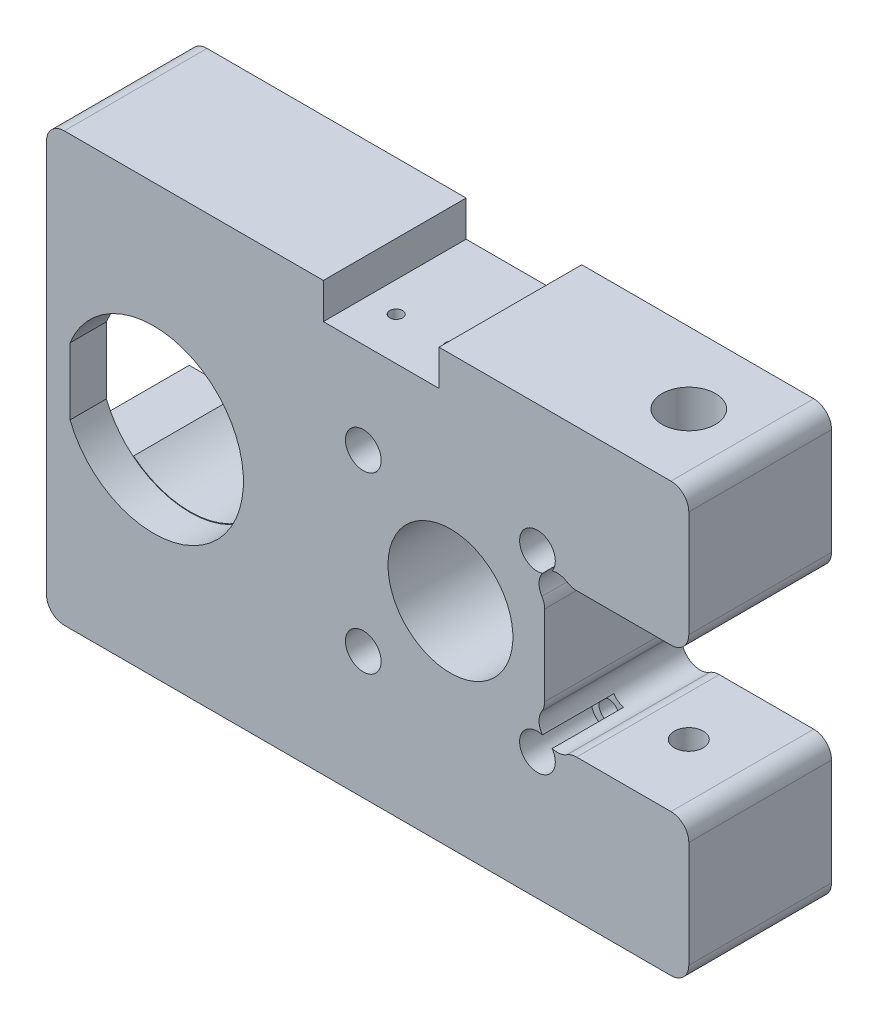
SolidWorks part; units mm, degrees
ref_plane "Front Plane" through (0, 0, 0) normal (0, 0, 1) x (1, 0, 0)
ref_plane "Top Plane" through (0, 0, 0) normal (0, 1, 0) x (1, 0, 0)
ref_plane "Right Plane" through (0, 0, 0) normal (1, 0, 0) x (0, 0, -1)
sketch "Sketch1" plane through (0, 0, 0) normal (0, 0, 1) x (1, 0, 0)
  line L1 (57.15, -38.1) -> (-57.15, -38.1)
  line L2 (57.15, -38.1) -> (57.15, 38.1)
  line L3 (57.15, 38.1) -> (-57.15, 38.1)
  line L4 (-57.15, -38.1) -> (-57.15, 38.1)
  line L5 (57.15, -38.1) -> (-57.15, 38.1) construction
  line L6 (57.15, 38.1) -> (-57.15, -38.1) construction
  point P0 (0, 0)
  dimension "D1" = 76.2
  dimension "D2" = 114.3
extrude "Boss-Extrude1" add sketch "Sketch1" along normal blind 25.4
sketch "Sketch2" plane through (0, 0, 25.4) normal (0, 0, 1) x (1, 0, 0)
  line L0 (-57.15, 38.1) -> (-57.15, -38.1) construction
  line L1 (57.15, 38.1) -> (-57.15, 38.1) construction
  line L2 (-53.975, 38.1) -> (-53.975, -38.1) construction
  line L3 (-57.15, -38.1) -> (57.15, -38.1) construction
  line L5 (-52.959, 5.9392) -> (-52.959, -5.9392)
  circle A1 centre (-38.1, 0) radius 15.875 construction
  arc A2 (-52.959, -5.9392) -> (-52.959, 5.9392) centre (-38.1, 0) ccw
  dimension "D2" = 16.002
  dimension "D3" = 31.75
  dimension "D4" = 1.016
  dimension "D1" = 3.175
extrude "Cut-Extrude1" cut sketch "Sketch2" against normal blind 6.477
sketch "Sketch3" plane through (0, 0, 18.923) normal (0, 0, 1) x (1, 0, 0)
  line L0 (-54.445, 0) -> (53.1859, 0) construction
  line L1 (-15.0726, 9.9464) -> (-12.8275, 12.1915) construction
  line L2 (-17.2768, 12.319) -> (-28.067, 12.319)
  line L3 (-57.15, 38.1) -> (-57.15, -38.1) construction
  line L4 (-15.0726, -9.9464) -> (-12.8275, -12.1915) construction
  line L5 (-48.133, -12.319) -> (-57.15, -12.319)
  line L6 (-17.2768, -12.319) -> (-28.067, -12.319)
  line L7 (-15.0726, 9.9464) -> (-23.9041, 9.9464) construction
  line L8 (-48.133, 12.319) -> (-57.15, 12.319)
  line L9 (-12.7, 7.7422) -> (-12.7, 13.9418) construction
  line L10 (-57.15, -12.319) -> (-57.15, 12.319)
  line L11 (-12.7, 7.7422) -> (-12.7, -7.7422)
  line L12 (-17.2768, 12.319) -> (-12.7, 12.319) construction
  line L13 (-12.7, 12.319) -> (-15.0726, 9.9464) construction
  arc A0 (-28.067, 12.319) -> (-48.133, 12.319) centre (-38.1, 0) ccw
  arc A1 (-12.7, 7.7422) -> (-17.2768, 12.319) centre (-15.0726, 9.9464) ccw
  arc A2 (-12.7, -7.7422) -> (-17.2768, -12.319) centre (-15.0726, -9.9464) cw
  arc A3 (-28.067, -12.319) -> (-48.133, -12.319) centre (-38.1, 0) cw
  point P3 (-31.623, 25.4)
  point P17 (-31.623, -25.4)
  point P23 (-12.7, 0)
  point P24 (-57.15, 0)
  dimension "D5" = 6.477
  dimension "D1" = 12.319
  dimension "D2" = 15.24
  dimension "D3" = 9.017
  dimension "D4" = 45
  dimension "D6" = 3.175
  dimension "D7" = 44.45
extrude "Cut-Extrude2" cut sketch "Sketch3" against normal up to vertex (18.923 mm away)
sketch "Sketch4" plane through (0, 38.1, 0) normal (0, 1, 0) x (1, 0, 0)
  line L0 (12.7, -25.4) -> (12.7, 0) construction
  line L1 (57.15, -25.4) -> (-57.15, -25.4) construction
  line L2 (57.15, 0) -> (-57.15, 0) construction
  line L3 (57.15, -25.4) -> (57.15, 0) construction
  line L5 (-7.874, 0) -> (12.7, 0)
  line L6 (-7.874, 0) -> (-7.874, -25.4)
  line L7 (-7.874, -25.4) -> (12.7, -25.4)
  line L8 (12.7, 0) -> (12.7, -25.4)
  line L9 (-7.874, 0) -> (12.7, -25.4) construction
  line L10 (-7.874, -25.4) -> (12.7, 0) construction
  point P8 (2.413, -12.7)
  dimension "D1" = 44.45
  dimension "D2" = 20.574
extrude "Cut-Extrude3" cut sketch "Sketch4" against normal blind 6.35
sketch "Sketch5" plane through (0, 0, 0) normal (0, 0, -1) x (-1, 0, 0)
  line L0 (0, 0) -> (-57.15, 0) construction
  line L2 (-57.15, -38.1) -> (-57.15, 38.1) construction
  line L3 (-33.7411, 10.5819) -> (-33.7411, -10.5819) construction
  line L4 (-36.0751, -12.827) -> (-57.15, -12.827)
  line L5 (-31.496, -8.2479) -> (-31.496, 8.2479)
  line L6 (-36.0751, 12.827) -> (-57.15, 12.827)
  line L7 (-57.15, -12.827) -> (-57.15, 12.827)
  line L8 (-31.496, -12.827) -> (-57.15, 12.827) construction
  line L9 (-31.496, 12.827) -> (-57.15, -12.827) construction
  line L10 (-57.15, 38.1) -> (-12.7, 38.1) construction
  line L11 (38.1, 0) -> (38.1, 30.2258) construction
  arc A0 (-36.0751, -12.827) -> (-31.496, -8.2479) centre (-33.7411, -10.5819) ccw
  arc A2 (-31.496, 8.2479) -> (-36.0751, 12.827) centre (-33.7411, 10.5819) ccw
  point P4 (-44.323, 0)
  dimension "D4" = 3.175
  dimension "D5" = 25.654
  dimension "D3" = 27.5181
  dimension "D1" = 25.654
  dimension "D2" = 25.654
  dimension "D6" = 23.4089
  dimension "D7" = 69.596
extrude "Cut-Extrude4" cut sketch "Sketch5" against normal up to vertex
sketch "Sketch6" plane through (0, 0, 0) normal (0, 0, -1) x (-1, 0, 0)
  line L0 (-14.732, 0) -> (0.768, 0) construction
  line L1 (-35.814, -21.082) -> (6.35, -21.082) construction
  line L2 (-35.814, -21.082) -> (-35.814, 21.082) construction
  line L3 (-35.814, 21.082) -> (6.35, 21.082) construction
  line L4 (6.35, -21.082) -> (6.35, 21.082) construction
  line L5 (-35.814, 21.082) -> (6.35, -21.082) construction
  line L6 (0, 0) -> (-58.0233, 0) construction
  line L7 (-57.15, 12.827) -> (-57.15, 38.1) construction
  line L8 (0.768, -15.5) -> (0.768, 15.5) construction
  line L9 (-31.496, -8.2479) -> (-31.496, 8.2479) construction
  line L10 (-30.22, -15.5) -> (-30.22, 15.488) construction
  line L11 (-30.22, -15.5) -> (0.768, -15.5) construction
  circle A0 centre (0.768, 15.5) radius 1.75
  circle A1 centre (0.768, -15.5) radius 1.75
  circle A2 centre (-14.732, 0) radius 11.1125
  circle A3 centre (-30.22, -15.5) radius 1.75
  circle A4 centre (-30.22, 15.488) radius 1.75
  point P0 (-14.732, 0)
  point P5 (-14.732, 0)
  dimension "D4" = 3.5
  dimension "D5" = 22.225
  dimension "D9" = 30.988
  dimension "D10" = 30.988
  dimension "D1" = 42.164
  dimension "D2" = 42.164
  dimension "D3" = 31
  dimension "D6" = 15.5
  dimension "D7" = 63.5
  dimension "D8" = 16.764
extrude "Cut-Extrude5" cut sketch "Sketch6" against normal up to vertex
sketch "Sketch8" plane through (0, 0, 25.4) normal (0, 0, 1) x (1, 0, 0)
  circle A0 centre (-0.768, -15.5) radius 3.175
  circle A1 centre (-0.768, 15.5) radius 3.175
  circle A2 centre (30.22, -15.5) radius 3.175
  circle A3 centre (30.22, 15.488) radius 3.175
  dimension "D1" = 6.35
extrude "Cut-Extrude6" cut sketch "Sketch8" against normal blind 12.7
fillet "Fillet1" radius 3.175 6 edges at (57.15, 38.1, 12.7) (57.15, -38.1, 12.7) (-57.15, -38.1, 12.7) (-57.15, 38.1, 12.7) (57.15, -12.827, 12.7) (57.15, 12.827, 12.7)
sketch "Sketch9" plane through (0, 38.1, 0) normal (0, 1, 0) x (1, 0, 0)
  line L0 (-53.975, -12.7) -> (53.975, -12.7) construction
  line L1 (-53.975, 0) -> (-53.975, -25.4) construction
  line L2 (53.975, -25.4) -> (53.975, 0) construction
  line L3 (57.15, 0) -> (57.15, -25.4) construction
  circle A0 centre (44.45, -12.7) radius 2.5797
  dimension "D1" = 5.1594
  dimension "D2" = 12.7
extrude "Cut-Extrude7" cut sketch "Sketch9" against normal up to vertex
sketch "Sketch10" plane through (0, 38.1, 0) normal (0, 1, 0) x (1, 0, 0)
  circle A0 centre (44.45, -12.7) radius 4.7625
  dimension "D1" = 9.525
extrude "Cut-Extrude8" cut sketch "Sketch10" against normal blind 15.875
sketch "Sketch11" plane through (0, -38.1, 0) normal (0, -1, 0) x (1, 0, 0)
  circle A0 centre (44.45, 12.7) radius 4.7625
  dimension "D1" = 9.525
extrude "Cut-Extrude9" cut sketch "Sketch11" against normal blind 15.875
fillet "Fillet2" radius 3.175 8 edges at (31.496, 8.2479, 12.7) (36.0751, 12.827, 12.7) (31.496, -8.2479, 12.7) (36.0751, -12.827, 12.7) (-17.2768, 12.319, 9.4615) (-12.7, 7.7422, 9.4615) (-12.7, -7.7422, 9.4615) (-17.2768, -12.319, 9.4615)
sketch "Sketch12" plane through (0, -38.1, 0) normal (0, -1, 0) x (1, 0, 0)
  line L0 (-12.7, -0.0353) -> (-12.7, 25.4) construction
  line L1 (57.15, -15.205) -> (57.15, 43.1612) construction
  line L2 (57.15, 25.4) -> (57.15, 0) construction
  line L3 (-53.975, 25.4) -> (53.975, 25.4) construction
  circle A0 centre (-6.35, 12.6823) radius 2.032
  dimension "D3" = 4.064
  dimension "D1" = 69.85
  dimension "D2" = 6.35
extrude "Cut-Extrude10" cut sketch "Sketch12" against normal blind 12.446
sketch "Sketch13" plane through (-57.15, 0, 0) normal (-1, 0, 0) x (0, 0, 1)
  line L0 (0, 0) -> (25.4, 0) construction
  line L1 (25.4, 34.925) -> (25.4, -34.925) construction
  line L2 (12.7, 28.575) -> (12.7, -28.575) construction
  line L3 (0, 38.1) -> (25.4, 38.1) construction
  circle A0 centre (12.7, 28.575) radius 1.3526
  circle A1 centre (12.7, -28.575) radius 1.3525
  point P9 (12.7, 0)
  dimension "D1" = 2.7051
  dimension "D2" = 9.525
extrude "Cut-Extrude11" cut sketch "Sketch13" against normal blind 12.7
sketch "Sketch14" plane through (0, 31.75, 0) normal (0, 1, 0) x (1, 0, 0)
  line L0 (-2.54, -17.78) -> (7.366, -17.78) construction
  line L1 (12.7, -25.4) -> (12.7, 0) construction
  circle A0 centre (-2.54, -17.78) radius 1.143
  circle A1 centre (7.366, -17.78) radius 1.143
  dimension "D1" = 2.286
  dimension "D2" = 9.906
  dimension "D3" = 7.62
  dimension "D4" = 5.334
extrude "Cut-Extrude12" cut sketch "Sketch14" against normal blind 12.7
